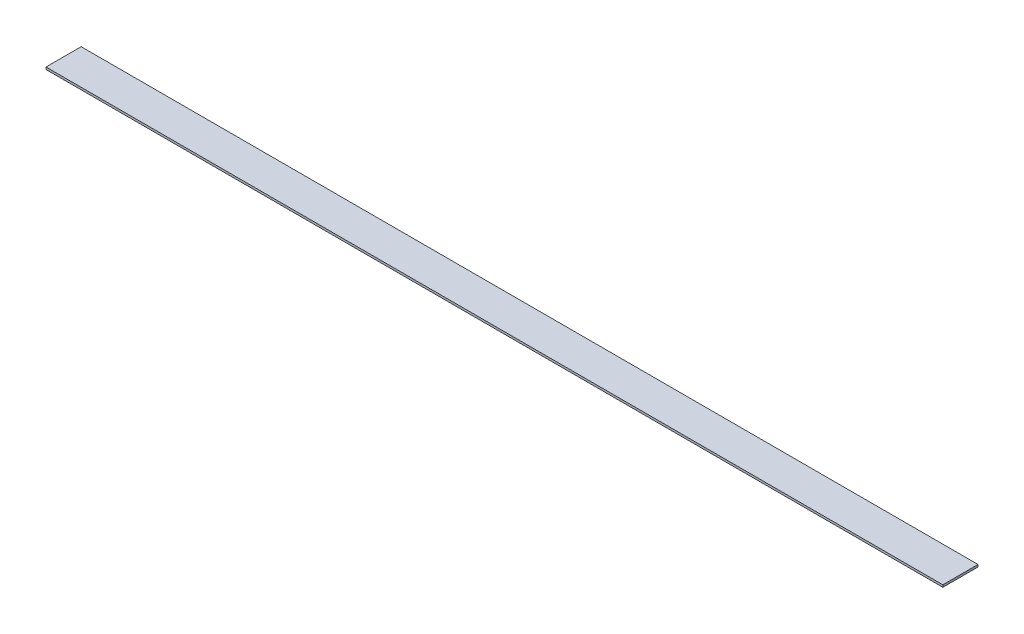
SolidWorks part; units mm, degrees
material "Pine"
ref_plane "Front Plane" through (0, 0, 0) normal (0, 0, 1) x (1, 0, 0)
ref_plane "Top Plane" through (0, 0, 0) normal (0, 1, 0) x (1, 0, 0)
ref_plane "Right Plane" through (0, 0, 0) normal (1, 0, 0) x (0, 0, -1)
sketch "Sketch1" plane through (0, 0, 0) normal (0, 1, 0) x (1, 0, 0)
  line L1 (-1295.4, 50.8) -> (1295.4, 50.8)
  line L2 (-1295.4, 50.8) -> (-1295.4, -50.8)
  line L3 (-1295.4, -50.8) -> (1295.4, -50.8)
  line L4 (1295.4, 50.8) -> (1295.4, -50.8)
  line L5 (-1295.4, 50.8) -> (1295.4, -50.8) construction
  line L6 (-1295.4, -50.8) -> (1295.4, 50.8) construction
  point P0 (0, 0)
  dimension "D1" = 101.6
  dimension "D2" = 2590.8
extrude "Boss-Extrude1" add sketch "Sketch1" along normal blind 6.35
